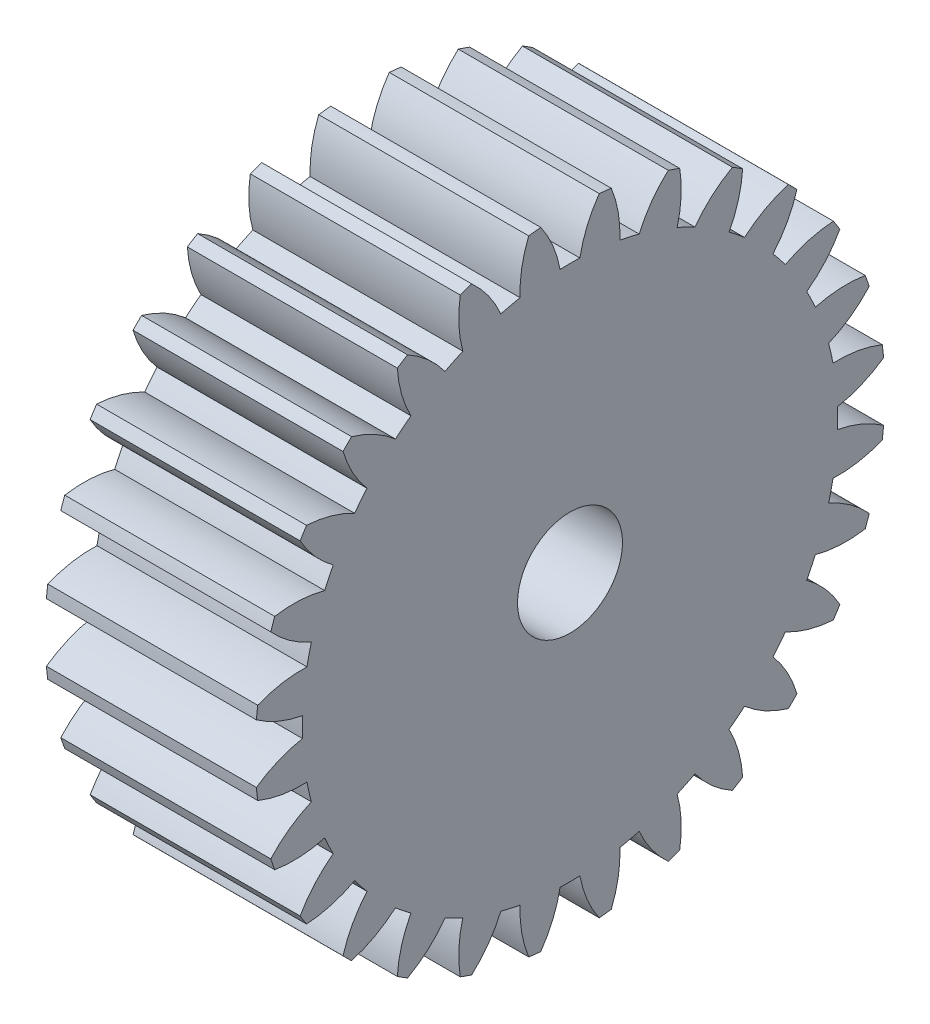
SolidWorks part; units mm, degrees
ref_plane "Plane1" through (0, 0, 0) normal (0, 0, 1) x (1, 0, 0)
ref_plane "Plane2" through (0, 0, 0) normal (0, 1, 0) x (1, 0, 0)
ref_plane "Plane3" through (0, 0, 0) normal (1, 0, 0) x (0, 0, -1)
other "Configuration Table"
sketch "HoldingSke" plane through (0, 0, 0) normal (0, 1, 0) x (1, 0, 0)
  line L0 (0, 0) -> (0.8829, -0.4695)
  line L1 (-15, 0) -> (100, 0) construction
  line L2 (0, 0) -> (-2.1039, 2.3779)
  line L3 (0, 0) -> (-11.863, 4.5341)
  line L4 (0, 0) -> (7.6251, 4.0544)
  line L5 (0, 0) -> (-46.8476, -17.4728)
  line L6 (0, 0) -> (-8.2896, -5.593)
  line L7 (-2.1039, 2.3779) -> (8.6586, 51.2059)
  line L8 (-76.2, 54.61) -> (-75.3, 54.61)
  line L9 (-71.009, 38.7566) -> (-53.1078, 45.2721)
  line L10 (-76.2, 71.12) -> (104.1128, 71.12)
  line L11 (0, 0) -> (-10, 0)
  line L12 (-76.2, 101.6) -> (-76.162, 101.6)
  line L13 (24.9733, 27.94) -> (52.9518, 28.4284)
  line L14 (24.9733, 27.94) -> (24.9743, 27.94)
  line L15 (24.9733, 27.94) -> (100.4006, 29.5858)
  line L16 (-63.627, -1) -> (-12.827, -1)
  circle A0 centre (0, 0) radius 2.5
  circle A1 centre (0, 0) radius 12.749
  circle A2 centre (0, 0) radius 37.5
  circle A3 centre (0, 0) radius 2.5
  dimension "MHD" = 25.498
  dimension "Hub_dia" = 75
  dimension "Bore" = 5
  dimension "MBD" = 5
  dimension "Num_teeth" = 28
  dimension "Pitch" = 1
  dimension "Overall_len" = 50
  dimension "Show_teeth" = 28
  dimension "Thickness" = 10
  dimension "OAL" = 50.0001
  dimension "T_dim" = 0.9
  dimension "Ap" = 20
  dimension "H" = 19.05
  dimension "Pitch_radius" = 180.3128
  dimension "Width" = 10
  dimension "Backlash" = 0.038
  dimension "Addendum_fac" = 1
  dimension "Dedendum_fac" = 1.25
  dimension "Clearance_fac" = 0.25
  dimension "Dedendum_add" = 0.001
  dimension "Module" = 1
sketch "BasProSke" plane through (0, 0, 0) normal (0, 1, 0) x (1, 0, 0)
  line L0 (-10, 0) -> (60, 0) construction
  line L1 (0, 0) -> (0, 15)
  line L2 (0, 0) -> (10, 0)
  line L3 (10, 0) -> (10, 15)
  line L4 (10, 15) -> (0, 15)
  dimension "Thickness" = 10
  dimension "Diameter" = 30
revolve "Base-Revolve" add sketch "BasProSke" angle 360 about L0
sketch "TooCutSke" plane through (0, 0, 0) normal (1, 0, 0) x (0, 0, -1)
  line L1 (0, 0) -> (0, 107) construction
  line L2 (0, 0) -> (-0.8515, 13.9741) construction
  line L3 (0, 0) -> (-3.1309, 27.7873) construction
  line L4 (-0.8515, 13.9741) -> (-1.5654, 13.8936) construction
  arc A0 (0.4713, 12.7403) -> (-0.4713, 12.7403) centre (0, 0) ccw
  arc A1 (1.4098, 14.9591) -> (-1.4098, 14.9591) centre (0, 0) ccw
  circle A2 centre (0, 0) radius 14 construction
  circle A3 centre (0, 0) radius 13.1557 construction
  arc A4 (-0.4713, 12.7403) -> (-1.4098, 14.9591) centre (-5.9775, 11.7193) ccw
  arc A5 (1.4098, 14.9591) -> (0.4713, 12.7403) centre (5.9775, 11.7193) ccw
  dimension "Root_dia" = 25.498
  dimension "Overcut_dia" = 30.0508
  dimension "Pitch_dia" = 28
  dimension "Base_dia" = 26.3114
  dimension "Flank_rad" = 5.6
  dimension "Half_ang" = 6.429
  dimension "Half_CT" = 0.7185
extrude "ToothCut" cut sketch "TooCutSke" along normal through all
fillet "Breaks" [suppressed] radius 0.02
fillet "RootFillets" [suppressed] radius 0.251
pattern_circular "TeethCuts" count 28 every 12.857 about axis through (-10, 0, 0) along (1, 0, 0) of "ToothCut", "RootFillets", "Breaks"
sketch "HubNeaOneSke" plane through (0, 0, 0) normal (-1, 0, 0) x (0, 0, 1)
  circle A0 centre (0, 0) radius 12.749
  dimension "Diameter" = 25.498
extrude "HubNearOne" [suppressed] add sketch "HubNeaOneSke" along normal blind 40.0001
sketch "HubNeaBotSke" plane through (0, 0, 0) normal (-1, 0, 0) x (0, 0, 1)
  circle A0 centre (0, 0) radius 12.749
  dimension "Diameter" = 25.498
extrude "HubNearBoth" [suppressed] add sketch "HubNeaBotSke" along normal blind 20
ref_plane "FarPln" through (10, 0, 0) normal (1, 0, 0) x (0, 0, -1)
sketch "HubFarSke" plane through (10, 0, 0) normal (1, 0, 0) x (0, 0, -1)
  circle A0 centre (0, 0) radius 12.749
  dimension "Diameter" = 25.498
extrude "HubFar" [suppressed] add sketch "HubFarSke" along normal blind 20
sketch "BorSke" plane through (0, 0, 0) normal (1, 0, 0) x (0, 0, -1)
  circle A0 centre (0, 0) radius 2.5
  dimension "Diameter" = 5
extrude "Bore" cut sketch "BorSke" along normal mid plane 100.0001
sketch "KeySke" plane through (0, 0, 0) normal (1, 0, 0) x (0, 0, -1)
  line L0 (-1, 0) -> (-1, 3.4)
  line L1 (-1, 3.4) -> (1, 3.4)
  line L2 (1, 3.4) -> (1, 0)
  line L3 (0, 0) -> (0, 34) construction
  line L4 (-1, 0) -> (1, 0)
  dimension "Offset" = 3.4
  dimension "Width" = 2
extrude "Keyway" [suppressed] cut sketch "KeySke" along normal mid plane 100.0001
pattern_circular "Keyway2" [suppressed] count 2 every 90 about axis through (-10, 0, 0) along (1, 0, 0)
equation "' \"Module@HoldingSke\" = 6.35"
equation "' \"Num_teeth@HoldingSke\" = 12"
equation "' \"Ap@HoldingSke\" =  20"
equation "' \"Ap@HoldingSke\" = 20"
equation "' \"Width@HoldingSke\" = 0.5 * 25.4"
equation "' \"Hub_dia@HoldingSke\"= 1 * 25.4"
equation "' \"Hub_dia@HoldingSke\" = 1 * 25.4"
equation "' \"Overall_len@HoldingSke\" = 1.0 * 25.4"
equation "' \"Bore@HoldingSke\" = 0.75 * 25.4"
equation "' \"T_dim@HoldingSke\" = 0.1 * 25.4"
equation "' \"Width@KeySke\" = 0.25 * 25.4"
equation "' \"Show_teeth@HoldingSke\" = 13"
equation "' \"Backlash@HoldingSke\" = 0.009 * 25.4"
equation "' \"Addendum_fac@HoldingSke\" = 1.0"
equation "' \"Dedendum_fac@HoldingSke\" = 1.25"
equation "' \"Dedendum_add@HoldingSke\" = 0.00005 * 25.4"
equation "' \"Clearance_fac@HoldingSke\" = 0.25"
equation "\"Pitch@HoldingSke\" = 1 / \"Module@HoldingSke\""
equation "\"Overcut_dia@TooCutSke\" = (\"Num_teeth@HoldingSke\" + 2 * \"Addendum_fac@HoldingSke\") / \"Pitch@HoldingSke\" + 0.002 * 25.4"
equation "\"Pitch_dia@TooCutSke\" = \"Num_teeth@HoldingSke\" / \"Pitch@HoldingSke\""
equation "\"Base_dia@TooCutSke\" = \"Num_teeth@HoldingSke\" / \"Pitch@HoldingSke\" * cos((\"Ap@HoldingSke\"  * 3.14159265 / 180))"
equation "\"Root_dia@TooCutSke\" = (\"Num_teeth@HoldingSke\" + 2) / \"Pitch@HoldingSke\" - 2 * (\"Addendum_fac@HoldingSke\" + \"Dedendum_fac@HoldingSke\") / \"Pitch@HoldingSke\" - \"Dedendum_add@HoldingSke\" * 2"
equation "\"Half_ang@TooCutSke\" = 180 / \"Num_teeth@HoldingSke\""
equation "\"Half_CT@TooCutSke\" = \"Num_teeth@HoldingSke\" / \"Pitch@HoldingSke\" * sin((3.14159265 / 2 / \"Num_teeth@HoldingSke\")) / 2 - 7 * \"Backlash@HoldingSke\" / 4"
equation "\"Flank_rad@TooCutSke\" = \"Num_teeth@HoldingSke\" / \"Pitch@HoldingSke\" / 5"
equation "\"Radius@RootFillets\" = \"Clearance_fac@HoldingSke\" / \"Pitch@HoldingSke\" + \"Dedendum_add@HoldingSke\""
equation "\"Break_rad@Breaks\" = 0.02 / \"Pitch@HoldingSke\""
equation "\"Thickness@HoldingSke\" = \"Width@HoldingSke\""
equation "\"OAL@HoldingSke\" = \"Thickness@HoldingSke\""
equation "\"MHD@HoldingSke\" = (\"Num_teeth@HoldingSke\" + 2) / \"Pitch@HoldingSke\" - 2 * (\"Addendum_fac@HoldingSke\" + \"Dedendum_fac@HoldingSke\")  / \"Pitch@HoldingSke\" - \"Dedendum_add@HoldingSke\" * 2"
equation "\"MBD@HoldingSke\" = (\"Num_teeth@HoldingSke\" + 2) / \"Pitch@HoldingSke\" - 2 * (\"Addendum_fac@HoldingSke\" + \"Dedendum_fac@HoldingSke\")  / \"Pitch@HoldingSke\" - \"Dedendum_add@HoldingSke\" * 2 - 0.002 * 25.4"
equation "\"MHD@HoldingSke\" = ((sgn( \"MHD@HoldingSke\" - \"Hub_dia@HoldingSke\" )-1)*( \"MHD@HoldingSke\" - \"Hub_dia@HoldingSke\" ))/-2+ \"Hub_dia@HoldingSke\""
equation "\"MBD@HoldingSke\" = ((sgn( \"MBD@HoldingSke\" - \"Bore@HoldingSke\" )-1)*( \"MBD@HoldingSke\" - \"Bore@HoldingSke\" ))/-2+ \"Bore@HoldingSke\""
equation "\"OAL@HoldingSke\" = ((sgn( \"OAL@HoldingSke\" - \"Overall_len@HoldingSke\" )+1)*( \"OAL@HoldingSke\" - \"Overall_len@HoldingSke\" ))/2 + \"Overall_len@HoldingSke\" + 0.000002 * 25.4"
equation "\"Num_teeth@TeethCuts\" = int( \"Show_teeth@HoldingSke\" ) + 1"
equation "\"Num_teeth@TeethCuts\" = ((sgn( \"Num_teeth@TeethCuts\" - \"Num_teeth@HoldingSke\" )-1)*( \"Num_teeth@TeethCuts\" - \"Num_teeth@HoldingSke\" ))/-2+ \"Num_teeth@HoldingSke\""
equation "\"Num_teeth@TeethCuts\" = ((sgn( \"Num_teeth@TeethCuts\" - 2.0)+1)*( \"Num_teeth@TeethCuts\" - 2.0))/2 +2.0"
equation "\"Angle@TeethCuts\" = 360.0 / \"Num_teeth@HoldingSke\""
equation "\"Diameter@BasProSke\" = (\"Num_teeth@HoldingSke\" + 2 * \"Addendum_fac@HoldingSke\") / \"Pitch@HoldingSke\""
equation "\"Thickness@BasProSke\"  = \"Thickness@HoldingSke\""
equation "' \"Fillet_rad@BasProSke\" =  \"Thickness@HoldingSke\" * 0.05"
equation "' \"Fillet_rad@BasProSke\" = \"Thickness@HoldingSke\" * 0.05"
equation "\"MHD@HoldingSke\" = ((sgn( \"MHD@HoldingSke\" - \"Root_dia@TooCutSke\" )-1)*( \"MHD@HoldingSke\" - \"Root_dia@TooCutSke\" ))/-2+ \"Root_dia@TooCutSke\""
equation "\"Diameter@HubNeaOneSke\" = \"MHD@HoldingSke\""
equation "\"Length@HubNearOne\" = \"OAL@HoldingSke\" - \"Thickness@BasProSke\""
equation "\"Diameter@HubNeaBotSke\" = \"MHD@HoldingSke\""
equation "\"Length@HubNearBoth\" = ( \"OAL@HoldingSke\" - \"Thickness@BasProSke\" ) / 2.0"
equation "\"Thickness@FarPln\" = \"Thickness@BasProSke\""
equation "\"Diameter@HubFarSke\" = \"MHD@HoldingSke\""
equation "\"Length@HubFar\" = ( \"OAL@HoldingSke\" - \"Thickness@BasProSke\" ) / 2.0"
equation "\"Diameter@BorSke\" = \"MBD@HoldingSke\""
equation "\"D1@Bore\" = \"OAL@HoldingSke\" * 2.0"
equation "\"D1@Keyway\" = \"OAL@HoldingSke\" * 2.0"
equation "\"Offset@KeySke\" = \"T_dim@HoldingSke\" + \"MBD@HoldingSke\" / 2.0"
